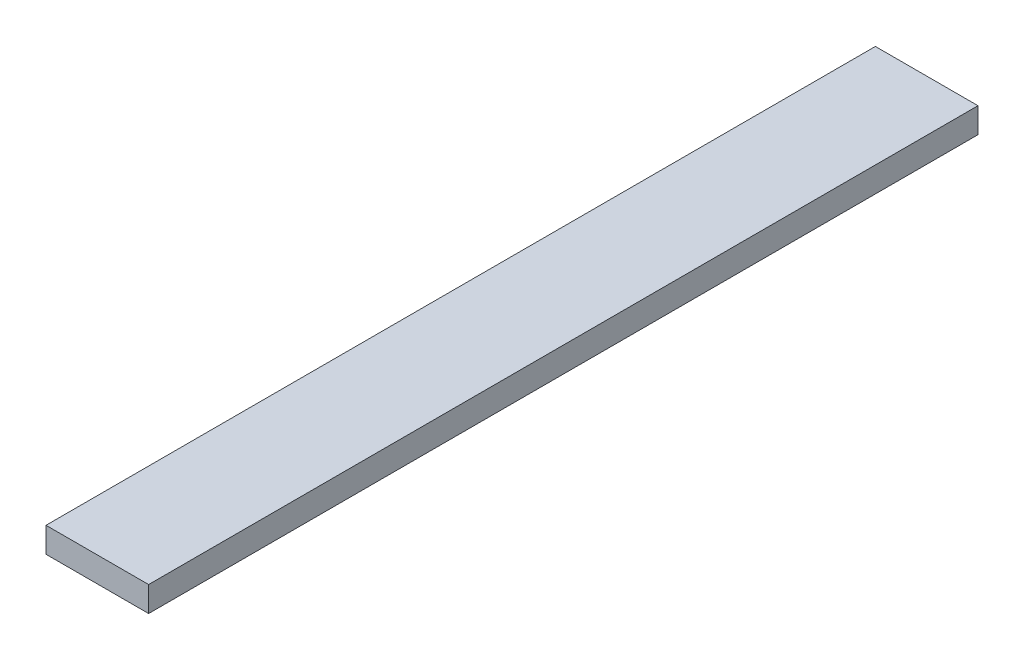
SolidWorks part; units mm, degrees
ref_plane "Front Plane" through (0, 0, 0) normal (0, 0, 1) x (1, 0, 0)
ref_plane "Top Plane" through (0, 0, 0) normal (0, 1, 0) x (1, 0, 0)
ref_plane "Right Plane" through (0, 0, 0) normal (1, 0, 0) x (0, 0, -1)
sketch "Sketch1" plane through (0, 0, 0) normal (0, 1, 0) x (1, 0, 0)
  line L1 (-57.0652, 166.4783) -> (-32.5652, 166.4783)
  line L2 (-57.0652, 166.4783) -> (-57.0652, -31.5217)
  line L3 (-57.0652, -31.5217) -> (-32.5652, -31.5217)
  line L4 (-32.5652, 166.4783) -> (-32.5652, -31.5217)
  dimension "D1" = 24.5
  dimension "D2" = 198
extrude "Boss-Extrude1" add sketch "Sketch1" along normal blind 6
